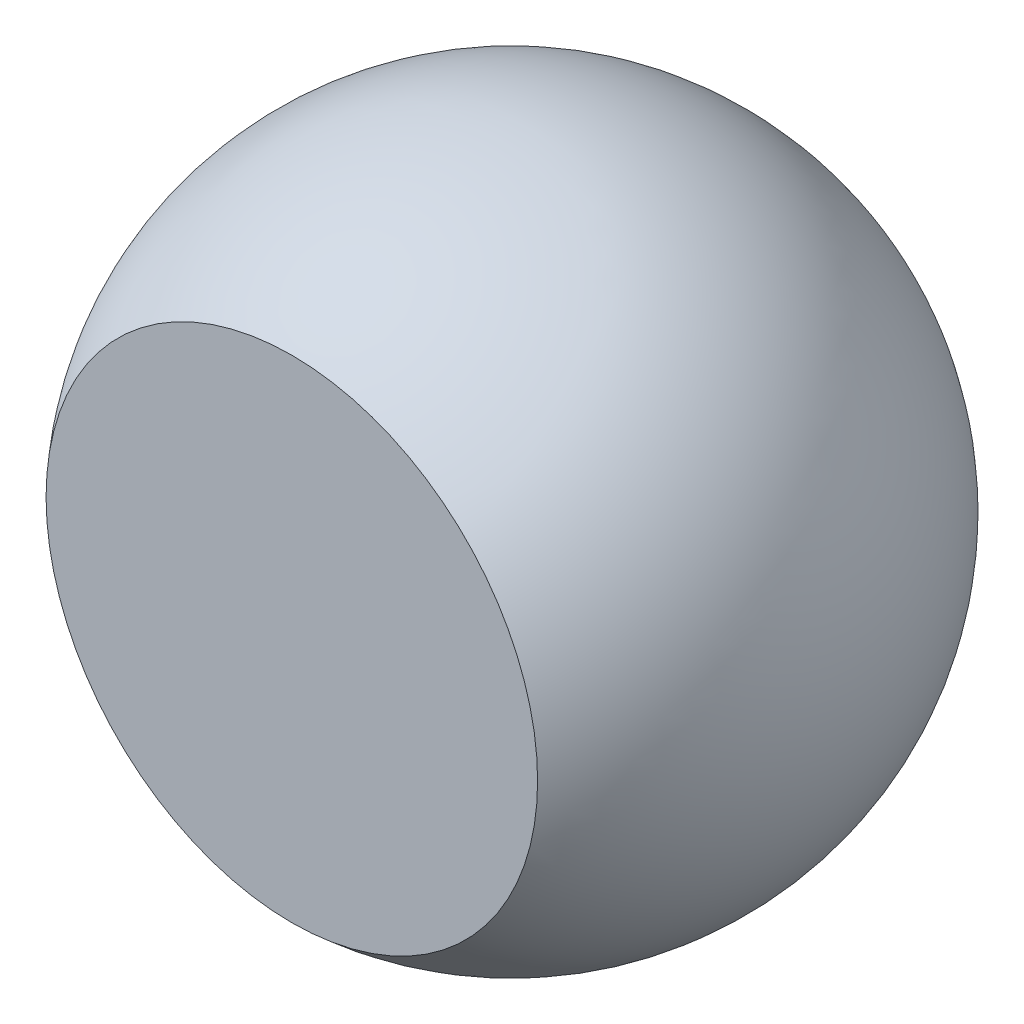
SolidWorks part; units mm, degrees
ref_plane "Спереди" through (0, 0, 0) normal (0, 0, 1) x (1, 0, 0)
ref_plane "Сверху" through (0, 0, 0) normal (0, 1, 0) x (1, 0, 0)
ref_plane "Справа" through (0, 0, 0) normal (1, 0, 0) x (0, 0, -1)
sketch "Эскиз1" plane through (0, 0, 0) normal (0, 1, 0) x (1, 0, 0)
  line L0 (0, 0.3) -> (0, -0.2)
  line L1 (0, 0.3773) -> (0, -0.3514) construction
  line L2 (0, -0.2) -> (0.2236, -0.2)
  arc A0 (0.2236, -0.2) -> (0, 0.3) centre (0, 0) ccw
  dimension "D1" = 0.2
  dimension "D2" = 0.3
revolve "Повернуть1" add sketch "Эскиз1" angle 360 about L1
